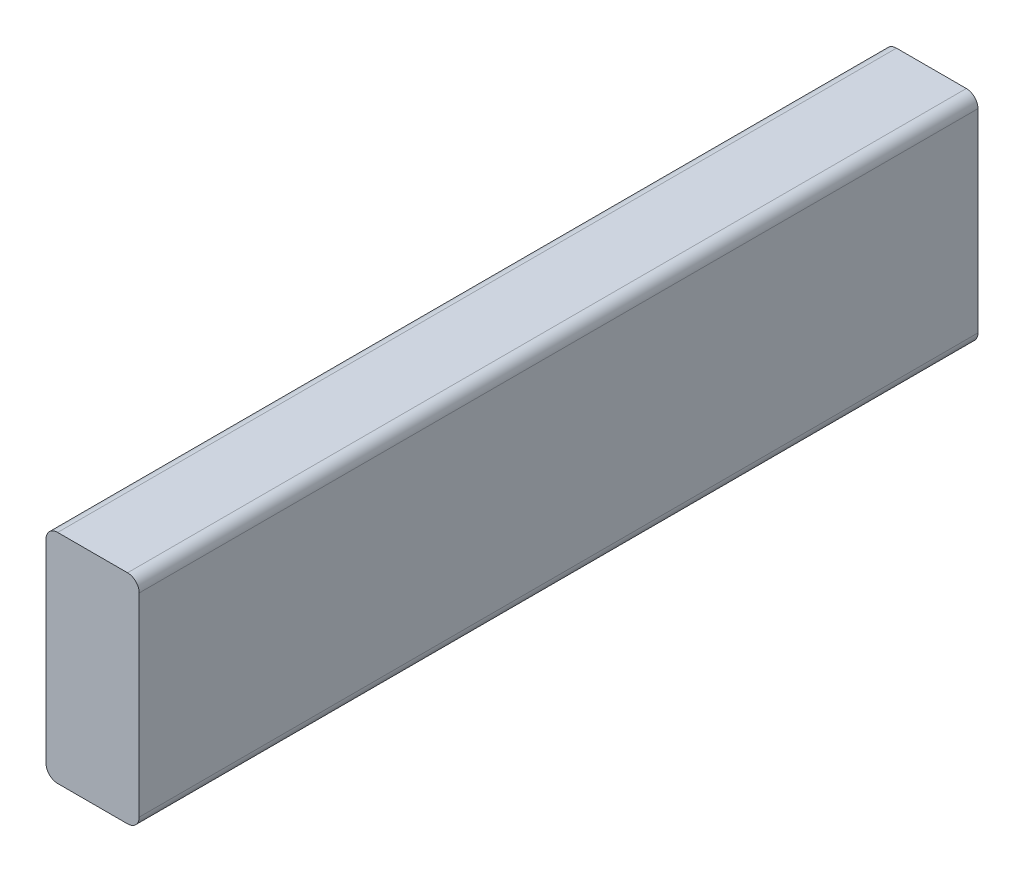
SolidWorks part; units mm, degrees
material "Pine"
ref_plane "Front Plane" through (0, 0, 0) normal (0, 0, 1) x (1, 0, 0)
ref_plane "Top Plane" through (0, 0, 0) normal (0, 1, 0) x (1, 0, 0)
ref_plane "Right Plane" through (0, 0, 0) normal (1, 0, 0) x (0, 0, -1)
sketch "Sketch1" plane through (0, 0, 0) normal (0, 0, 1) x (1, 0, 0)
  line L1 (223.4883, 1473.2) -> (261.5883, 1473.2)
  line L2 (223.4883, 1473.2) -> (223.4883, 1384.3)
  line L3 (223.4883, 1384.3) -> (261.5883, 1384.3)
  line L4 (261.5883, 1473.2) -> (261.5883, 1384.3)
extrude "Boss-Extrude1" add sketch "Sketch1" against normal up to surface (342.9 mm away)
fillet "Fillet1" radius 4.7625 4 edges at (223.4883, 1473.2, -171.45) (223.4883, 1384.3, -171.45) (261.5883, 1384.3, -171.45) (261.5883, 1473.2, -171.45)
